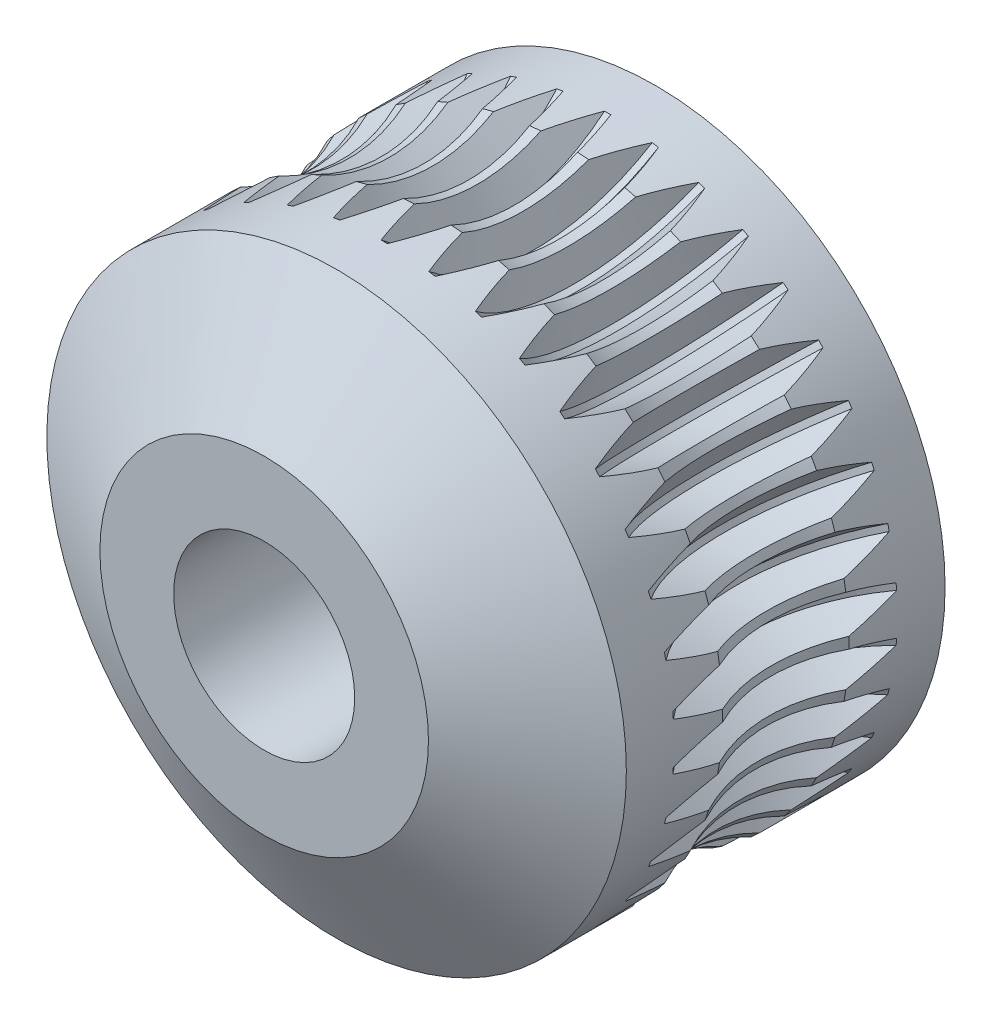
SolidWorks part; units mm, degrees
ref_plane "Front Plane" through (0, 0, 0) normal (0, 0, 1) x (1, 0, 0)
ref_plane "Top Plane" through (0, 0, 0) normal (0, 1, 0) x (1, 0, 0)
ref_plane "Right Plane" through (0, 0, 0) normal (1, 0, 0) x (0, 0, -1)
sketch "Sketch1" plane through (0, 0, 0) normal (0, 0, 1) x (1, 0, 0)
  circle A0 centre (0, 0) radius 4
  circle A1 centre (0, 0) radius 1.25
  dimension "D1" = 8
  dimension "D2" = 2.5
extrude "Boss-Extrude1" add sketch "Sketch1" along normal blind 6.4
chamfer "Chamfer1" distance 1 angle 60 1 edges at (4, 0, 6.4)
ref_plane "Plane1" through (0, 0, 3.2) normal (0, 0, -1) x (-1, 0, 0)
sketch "Sketch2" plane through (0, 0, 0) normal (1, 0, 0) x (0, 0, -1)
  line L0 (-3.2, -3.3) -> (-3.2, 3.3) construction
  line L1 (0, 0) -> (-12.0979, 0) construction
  circle A0 centre (-3.2, 5.8) radius 2
  dimension "D1" = 4
  dimension "D2" = 5.8
revolve "Cut-Revolve1" cut sketch "Sketch2" angle 360 about L1
sketch "Sketch3" plane through (3.2, 0, 3.2) normal (0, 0, 1) x (1, 0, 0)
  line L0 (-3.2, 3.43) -> (-3.2, 3.8) construction
  line L1 (-3.4574, 3.8) -> (-2.9426, 3.8) construction
  line L2 (-5.0425, 5.8) -> (-2.1511, 5.8) construction
  line L3 (-3.2437, 3.43) -> (-3.1562, 3.43)
  line L4 (-3.1562, 3.43) -> (-2.9426, 3.8)
  line L5 (-2.9426, 3.8) -> (-2.1511, 3.8)
  line L6 (-2.1511, 3.8) -> (-2.1511, 4.3976)
  line L7 (-2.1511, 4.3976) -> (-4.2489, 4.3976)
  line L8 (-4.2489, 4.3976) -> (-4.2489, 3.8)
  line L9 (-4.2489, 3.8) -> (-3.4574, 3.8)
  line L10 (-3.4574, 3.8) -> (-3.2437, 3.43)
  point P15 (-3.2, 0)
  dimension "D1" = 2
  dimension "D2" = 5.8
  dimension "D3" = 0.0875
  dimension "D4" = 0.37
  dimension "D5" = 60
revolve "Cut-Revolve2" cut sketch "Sketch3" angle 360 about L2
ref_axis "Axis1" through (0, 0, 6.4) along (0, 0, -1)
pattern_circular "CirPattern1" count 38 over 360 about axis through (0, 0, 6.4) along (0, 0, -1) of "Cut-Revolve2"
chamfer "Chamfer2" distance 1 angle 60 1 edges at (4, 0, 0)
equation "\"D2@Sketch2\"=(7.6+4)/2"
